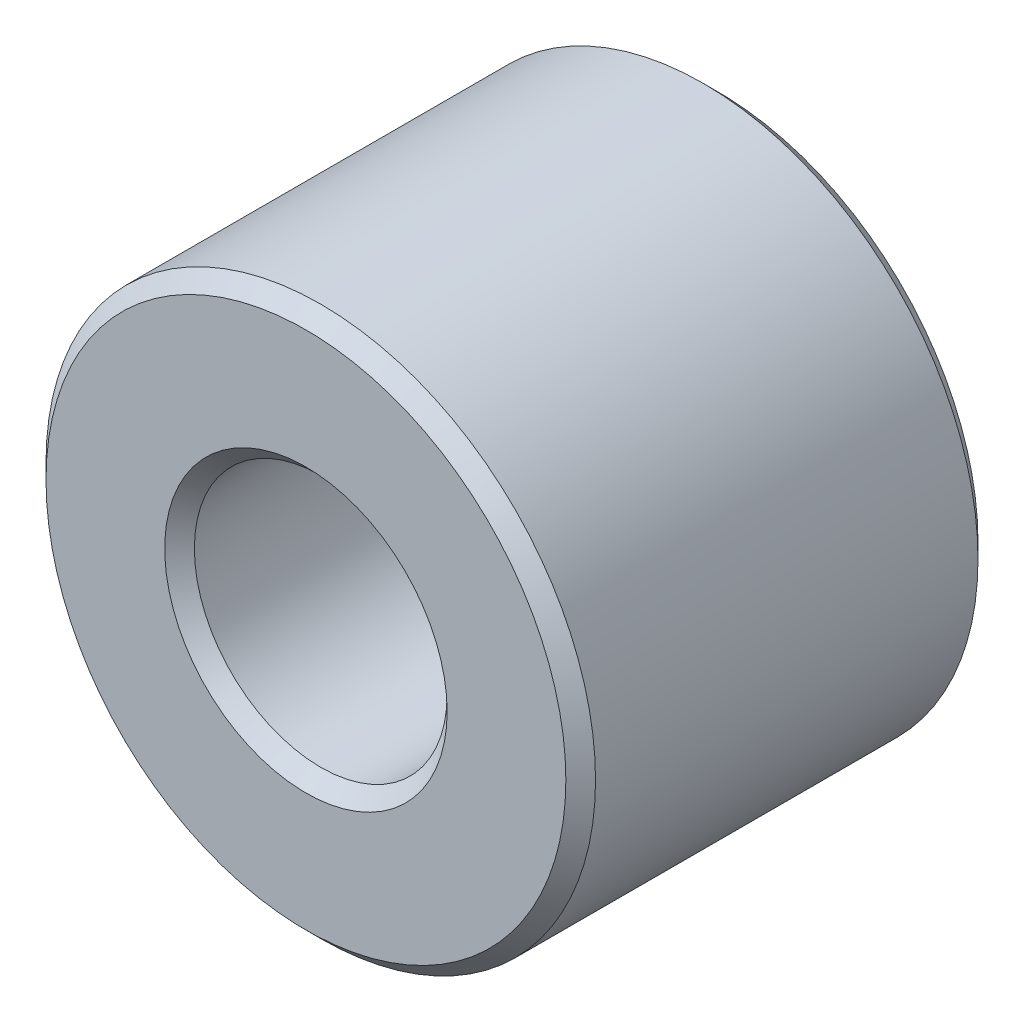
SolidWorks part; units mm, degrees
ref_plane "Front Plane" through (0, 0, 0) normal (0, 0, 1) x (1, 0, 0)
ref_plane "Top Plane" through (0, 0, 0) normal (0, 1, 0) x (1, 0, 0)
ref_plane "Right Plane" through (0, 0, 0) normal (1, 0, 0) x (0, 0, -1)
sketch "Sketch1" plane through (0, 0, 0) normal (0, 0, 1) x (1, 0, 0)
  circle A0 centre (0, 0) radius 3.175 construction
  circle A1 centre (0, 0) radius 1.4605 construction
  point P4 (0, 3.175)
  dimension "ID" = 2.921
  dimension "OD" = 6.35
sketch "Sketch2" plane through (0, 0, 0) normal (1, 0, 0) x (0, 0, -1)
  line L0 (-2.3812, 3.175) -> (2.3812, 3.175) construction
  dimension "Length" = 4.7625
sketch "Sketch3" plane through (0, 0, 0) normal (0, 0, 1) x (1, 0, 0)
  circle A0 centre (0, 0) radius 1.4605 construction
  circle A1 centre (0, 0) radius 3.175 construction
  circle A2 centre (0, 0) radius 1.4605
  circle A3 centre (0, 0) radius 3.175
extrude "Boss-Extrude1" add sketch "Sketch3" against normal up to vertex (2.3813 mm away) and the other way up to vertex (2.3813 mm away) up to point (0, 3.175, -2.3812) other way up to point (0, 3.175, 2.3812)
chamfer "Chamfer1" distance 0.1714 angle 45 4 edges at (3.175, 0, 2.3812) (3.175, 0, -2.3812) (1.4605, 0, 2.3812) (1.4605, 0, -2.3812)
equation "\"D1@Chamfer1\"=(\"OD@Sketch1\"-\"ID@Sketch1\")*0.05"
